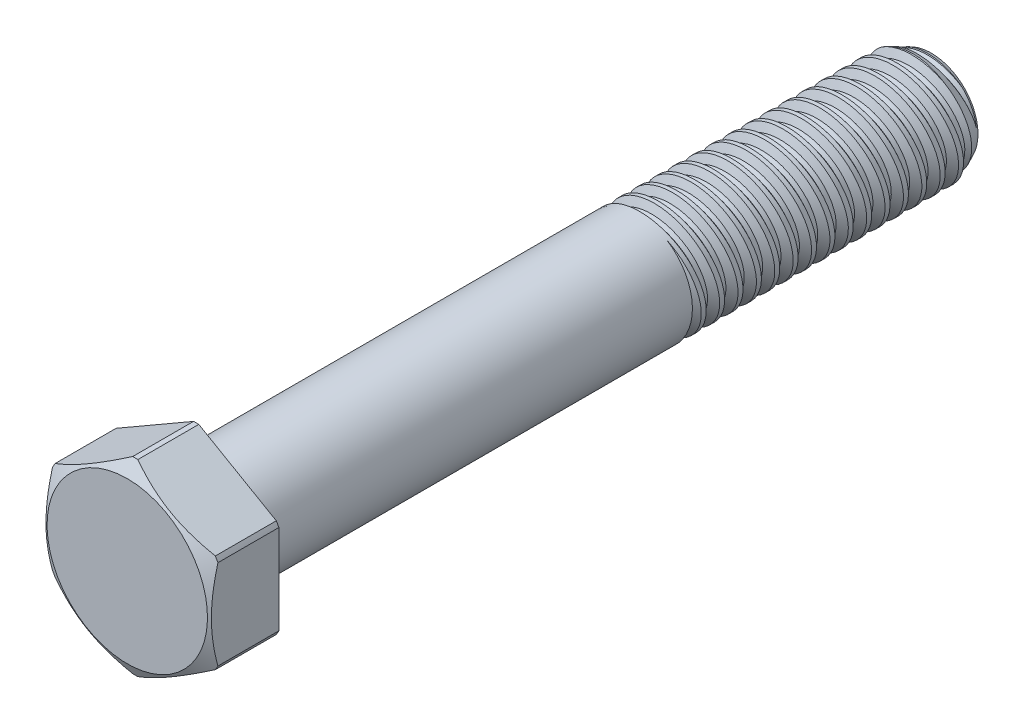
SolidWorks part; units mm, degrees
material "Plain Carbon Steel"
ref_plane "Front" through (0, 0, 0) normal (0, 0, 1) x (1, 0, 0)
ref_plane "Top" through (0, 0, 0) normal (0, 1, 0) x (1, 0, 0)
ref_plane "Right" through (0, 0, 0) normal (1, 0, 0) x (0, 0, -1)
sketch "Sketch1" plane through (0, 0, 0) normal (1, 0, 0) x (0, 0, -1)
  line L0 (0, 0) -> (-38.1, 0) construction
  line L1 (-38.1, 0) -> (-38.1, 7.1437) construction
  line L2 (-38.1, 0) -> (-44.0531, 0) construction
  line L3 (0, -4.7625) -> (25.4, -4.7625) construction
  line L4 (0, 0) -> (25.4, 0)
  line L5 (0, 0) -> (0, 4.7625)
  line L6 (0, 4.7625) -> (25.4, 4.7625)
  line L7 (25.4, 0) -> (25.4, 4.7625)
  dimension "Screw Dia" = 9.525
  dimension "Min Thread Length" = 25.4
  dimension "Screw Length" = 63.5
  dimension "Head Height" = 5.9531
  dimension "Head Width" = 14.2875
revolve "Revolve1" add sketch "Sketch1" angle 360 about L0
sketch "Sketch2" plane through (0, 0, 0) normal (1, 0, 0) x (0, 0, -1)
  line L0 (0, 4.7625) -> (0, -4.7625) construction
  line L1 (0, -4.7625) -> (1.5875, -4.7625) construction
  line L2 (1.5875, -4.7625) -> (0, 4.7625) construction
  line L3 (0, 4.7625) -> (0.1957, 4.7951) construction
  line L4 (1.5659, 5.0235) -> (0.1957, 4.7951)
  line L5 (0.1957, 4.7951) -> (0.8263, 4.0291)
  line L6 (0.8263, 4.0291) -> (1.2178, 4.0944)
  line L7 (1.2178, 4.0944) -> (1.5659, 5.0235)
  line L8 (1.0221, 4.0617) -> (0.8808, 4.9093) construction
  line L9 (0, 0) -> (0, 4.7625) construction
  line L10 (0, 4.7625) -> (0.9053, 4.7625) construction
  line L11 (0.9053, 4.7625) -> (2.4928, -4.7625) construction
  line L12 (2.4928, -4.7625) -> (1.5875, -4.7625) construction
  line L13 (0, -4.7625) -> (25.4, -4.7625) construction
  line L14 (0, -0.2832) -> (3.3981, 0.2832) construction
  line L15 (0, 4.7625) -> (25.4, 4.7625) construction
  point P17 (1.699, 0)
  dimension "D1" = 1.5875
  dimension "Thread Pitch" = 1.5875
  dimension "D3" = 0.3969
  dimension "D4" = 0.1984
  dimension "D5" = 60
revolve "Cut-Revolve1" cut sketch "Sketch2" angle 360 about L14
sketch "Sketch3" plane through (0, 0, 0) normal (1, 0, 0) x (0, 0, -1)
  line L0 (23.8272, 4.7625) -> (25.4, 4.0291)
  line L1 (25.4, 4.0291) -> (25.4, 4.7625)
  line L2 (25.4, 4.7625) -> (23.8272, 4.7625)
  line L3 (0, 4.7625) -> (25.4, 4.7625) construction
  line L4 (25.4, 0) -> (25.4, 4.7625) construction
  line L5 (0.8263, 4.0291) -> (25.4, 4.0291) construction
  line L6 (23.8272, 4.7625) -> (23.8272, -4.7625) construction
  line L7 (0, -4.7625) -> (25.4, -4.7625) construction
  line L8 (0, 0) -> (23.8272, 0) construction
  dimension "D1" = 25
  dimension "D2" = 9.525
revolve "Cut-Revolve2" cut sketch "Sketch3" angle 360 about L8
pattern_linear "LPattern1" count 2 spacing 1.5875 along (0, 0, 1) count 16 spacing 1.5875 along (0, 0, 1)
sketch "Sketch4" plane through (0, 0, 0) normal (1, 0, 0) x (0, 0, -1)
  line L0 (-38.1, 0) -> (-38.1, 7.1437) construction
  line L1 (0, 0) -> (-38.1, 0)
  line L2 (0, 0) -> (0, 4.7625)
  line L3 (0, 4.7625) -> (-38.1, 4.7625)
  line L4 (-38.1, 0) -> (-38.1, 4.7625)
  line L5 (0, 4.7625) -> (25.4, 4.7625) construction
  line L6 (-38.1, 0) -> (-44.0531, 0) construction
revolve "Revolve2" add sketch "Sketch4" angle 360 about L6
sketch "Sketch5" plane through (0, 0, 38.1) normal (0, 0, 1) x (1, 0, 0)
  line L1 (0, 8.2489) -> (-7.1437, 4.1244)
  line L2 (-7.1437, 4.1244) -> (-7.1437, -4.1244)
  line L3 (-7.1437, -4.1244) -> (0, -8.2489)
  line L4 (0, -8.2489) -> (7.1437, -4.1244)
  line L5 (7.1437, -4.1244) -> (7.1437, 4.1244)
  line L6 (7.1437, 4.1244) -> (0, 8.2489)
  circle A0 centre (0, 0) radius 7.1437 construction
  dimension "D1" = 14.2875
extrude "Extrude1" add sketch "Sketch5" along normal up to vertex
sketch "Sketch6" plane through (0, 0, 0) normal (1, 0, 0) x (0, 0, -1)
  line L0 (-44.0531, 6.9294) -> (-43.3647, 8.1219)
  line L1 (-43.3647, 8.1219) -> (-38.1, 8.1219)
  line L2 (-38.1, 8.1219) -> (-38.1, 8.6299)
  line L3 (-38.1, 8.6299) -> (-44.0531, 8.6299)
  line L4 (-44.0531, 8.6299) -> (-44.0531, 6.9294)
  line L5 (-44.0531, 4.1244) -> (-44.0531, 8.2489) construction
  line L6 (-44.0531, 8.2489) -> (-38.1, 8.2489) construction
  line L7 (-38.1, 4.1244) -> (-38.1, 8.2489) construction
  line L8 (0, 0) -> (-43.3647, 0) construction
  line L9 (-38.1, 0) -> (-44.0531, 0) construction
  line L10 (-43.3647, 0) -> (-43.3647, 8.1219) construction
  line L11 (-41.0766, 8.6299) -> (-41.0766, 0) construction
  dimension "D1" = 30
  dimension "D2" = 0.127
  dimension "D3" = 0.508
  dimension "D4" = 13.8589
  dimension "D5" = 5.9531
  dimension "D6" = 63.5
revolve "Cut-Revolve3" cut sketch "Sketch6" angle 360 about L8
fillet "Fillet1" radius 0.9525
equation "\"D3@Sketch2\"=\"Thread Pitch@Sketch2\"/4"
equation "\"D4@Sketch2\"=\"Thread Pitch@Sketch2\"/8"
equation "\"D1@Sketch2\"=\"Thread Pitch@Sketch2\""
equation "\"D3@LPattern1\"=\"Thread Pitch@Sketch2\""
equation "\"D4@LPattern1\"=\"Thread Pitch@Sketch2\""
equation "\"D2@LPattern1\"=\"Min Thread Length@Sketch1\"/\"Thread Pitch@Sketch2\""
equation "\"D4@Sketch6\"=\"Head Width@Sketch1\"*.97"
equation "\"D1@Fillet1\"=\"Screw Dia@Sketch1\"/10"
